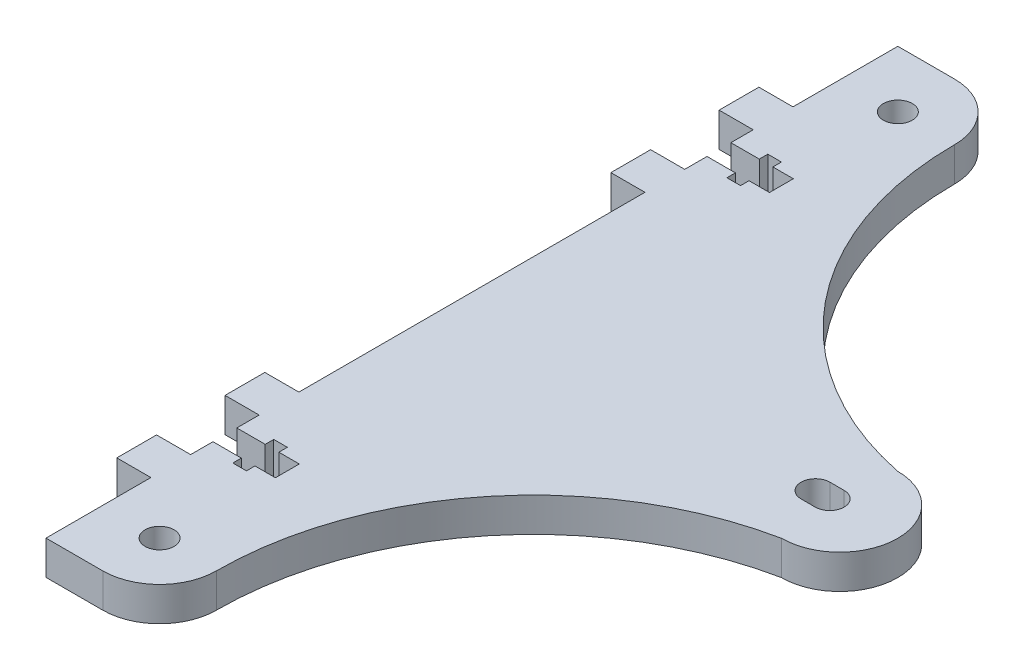
SolidWorks part; units mm, degrees
material "Клен"
ref_plane "Спереди" through (0, 0, 0) normal (0, 0, 1) x (1, 0, 0)
ref_plane "Сверху" through (0, 0, 0) normal (0, 1, 0) x (1, 0, 0)
ref_plane "Справа" through (0, 0, 0) normal (1, 0, 0) x (0, 0, -1)
sketch "Эскиз1" plane through (0, 0, 0) normal (0, 1, 0) x (1, 0, 0)
  line L0 (-41.181, -0.0464) -> (44.1026, -0.0464) construction
  line L9 (-35, -65) -> (-35, -75)
  line L11 (-35, -65) -> (-35, 65)
  line L12 (-35, -75) -> (-25, -75)
  line L14 (-35, 65) -> (-35, 75)
  line L15 (-35, 75) -> (-25, 75)
  arc A8 (-25, 75) -> (-15, 65) centre (-25, 65) cw
  arc A9 (-25, -75) -> (-15, -65) centre (-25, -65) ccw
  arc A10 (29.8091, 10.176) -> (29.8091, -10.2688) centre (29.8091, -0.0464) cw
  arc A13 (-15, -65) -> (29.8091, -10.2688) centre (40.8297, -65) cw
  arc A14 (-15, 65) -> (29.8091, 10.176) centre (40.9431, 65) ccw
  point P0 (0, 0)
extrude "Бобышка-Вытянуть1" add sketch "Эскиз1" along normal blind 6
sketch "Эскиз2" plane through (0, 0, 0) normal (0, -1, 0) x (1, 0, 0)
  line L4 (28, 0) -> (25.5, 0) construction
  line L5 (28, -2.55) -> (25.5, -2.55)
  line L6 (-46.1924, 0) -> (55.6646, 0) construction
  line L7 (28, 2.55) -> (25.5, 2.55)
  circle A0 centre (-25, -65) radius 2.55
  circle A5 centre (-25, 65) radius 2.55
  arc A6 (28, -2.55) -> (28, 2.55) centre (28, 0) ccw
  arc A7 (25.5, 2.55) -> (25.5, -2.55) centre (25.5, 0) ccw
  arc A8 (-25, -75) -> (-15, -65) centre (-25, -65) ccw construction
  point P13 (26.75, 0)
  dimension "D1" = 5.1
  dimension "D7" = 5.1
  dimension "D8" = 2.5
  dimension "D9" = 53
extrude "Вырез-Вытянуть1" cut sketch "Эскиз2" against normal through all
sketch "Эскиз21" plane through (15, 6, -43.5) normal (0, 1, 0) x (0, 0, -1)
  line L1 (-13.0318, 50) -> (-6.0318, 50)
  line L2 (-13.0318, 50) -> (-13.0318, 56)
  line L3 (-13.0318, 56) -> (-6.0318, 56)
  line L4 (-6.0318, 50) -> (-6.0318, 56)
  line L5 (13, 56) -> (-13, 56) construction
  line L6 (0, 53.4074) -> (0, -162.0434) construction
  line L7 (13.0318, 50) -> (6.0318, 50)
  line L8 (6.0318, 50) -> (6.0318, 56)
  line L9 (13.0318, 56) -> (6.0318, 56)
  line L10 (13.0318, 50) -> (13.0318, 56)
  dimension "D1" = 7
extrude "Бобышка-Вытянуть2" add sketch "Эскиз21" against normal blind 6
sketch "Эскиз31" plane through (15, 6, -43.5) normal (0, 1, 0) x (0, 0, -1)
  line L3 (-2.1, 45) -> (-3.6, 45)
  line L4 (-3.6, 45) -> (-3.6, 42.6)
  line L5 (-3.6, 42.6) -> (-2.1, 42.6)
  line L8 (0, 53.4074) -> (0, -162.0434) construction
  line L11 (3.6, 42.6) -> (2.1, 42.6)
  line L12 (3.6, 45) -> (3.6, 42.6)
  line L13 (2.1, 45) -> (3.6, 45)
  line L16 (-2.1, 45) -> (-2.1, 50)
  line L17 (-2.1, 50) -> (2.1, 50)
  line L18 (2.1, 50) -> (2.1, 45)
  line L19 (2.1, 42.6) -> (2.1, 39)
  line L20 (2.1, 39) -> (-2.1, 39)
  line L21 (-2.1, 39) -> (-2.1, 42.6)
  point P15 (0, 43.65)
  point P20 (0, 50)
  dimension "D2" = 7.2
  dimension "D3" = 2.4
  dimension "D4" = 4.2
extrude "Вырез-Вытянуть11" cut sketch "Эскиз31" against normal through all
other "Авто-элемент1<DIN967-4>"
sketch "Эскиз22" plane through (15, 0, -43.5) normal (0, -1, 0) x (0, 0, 1)
  line L1 (-13.0318, 50) -> (-6.0318, 50)
  line L2 (-13.0318, 50) -> (-13.0318, 56)
  line L3 (-13.0318, 56) -> (-6.0318, 56)
  line L4 (-6.0318, 50) -> (-6.0318, 56)
  line L5 (13, 56) -> (-13, 56) construction
  line L6 (0, 53.4074) -> (0, -162.0434) construction
  line L7 (13.0318, 50) -> (6.0318, 50)
  line L8 (6.0318, 50) -> (6.0318, 56)
  line L9 (13.0318, 56) -> (6.0318, 56)
  line L10 (13.0318, 50) -> (13.0318, 56)
  dimension "D1" = 7
extrude "Бобышка-Вытянуть21" add sketch "Эскиз22" against normal blind 6
other "Авто-элемент2<DIN967-5>"
sketch "Эскиз24" plane through (15, 0, 43.5) normal (0, -1, 0) x (0, 0, 1)
  line L1 (-13.0318, 50) -> (-6.0318, 50)
  line L2 (-13.0318, 50) -> (-13.0318, 56)
  line L3 (-13.0318, 56) -> (-6.0318, 56)
  line L4 (-6.0318, 50) -> (-6.0318, 56)
  line L5 (13, 56) -> (-13, 56) construction
  line L6 (0, 53.4074) -> (0, -162.0434) construction
  line L7 (13.0318, 50) -> (6.0318, 50)
  line L8 (6.0318, 50) -> (6.0318, 56)
  line L9 (13.0318, 56) -> (6.0318, 56)
  line L10 (13.0318, 50) -> (13.0318, 56)
  dimension "D1" = 7
extrude "Бобышка-Вытянуть23" add sketch "Эскиз24" against normal blind 6
sketch "Эскиз34" plane through (15, 0, 43.5) normal (0, -1, 0) x (0, 0, 1)
  line L3 (-2.1, 45) -> (-3.6, 45)
  line L4 (-3.6, 45) -> (-3.6, 42.6)
  line L5 (-3.6, 42.6) -> (-2.1, 42.6)
  line L8 (0, 53.4074) -> (0, -162.0434) construction
  line L11 (3.6, 42.6) -> (2.1, 42.6)
  line L12 (3.6, 45) -> (3.6, 42.6)
  line L13 (2.1, 45) -> (3.6, 45)
  line L16 (-2.1, 45) -> (-2.1, 50)
  line L17 (-2.1, 50) -> (2.1, 50)
  line L18 (2.1, 50) -> (2.1, 45)
  line L19 (2.1, 42.6) -> (2.1, 39)
  line L20 (2.1, 39) -> (-2.1, 39)
  line L21 (-2.1, 39) -> (-2.1, 42.6)
  point P15 (0, 43.65)
  point P20 (0, 50)
  dimension "D2" = 7.2
  dimension "D3" = 2.4
  dimension "D4" = 4.2
extrude "Вырез-Вытянуть14" cut sketch "Эскиз34" against normal through all
other "Авто-элемент4<DIN967-6>"
sketch "Эскиз25" plane through (15, 6, 43.5) normal (0, 1, 0) x (0, 0, -1)
  line L1 (-13.0318, 50) -> (-6.0318, 50)
  line L2 (-13.0318, 50) -> (-13.0318, 56)
  line L3 (-13.0318, 56) -> (-6.0318, 56)
  line L4 (-6.0318, 50) -> (-6.0318, 56)
  line L5 (13, 56) -> (-13, 56) construction
  line L6 (0, 53.4074) -> (0, -162.0434) construction
  line L7 (13.0318, 50) -> (6.0318, 50)
  line L8 (6.0318, 50) -> (6.0318, 56)
  line L9 (13.0318, 56) -> (6.0318, 56)
  line L10 (13.0318, 50) -> (13.0318, 56)
  dimension "D1" = 7
extrude "Бобышка-Вытянуть24" add sketch "Эскиз25" against normal blind 6
other "Авто-элемент5<DIN967-7>"
sketch "Эскиз26" plane through (15, 6, -43.5) normal (0, 1, 0) x (0, 0, -1)
  line L1 (-13.0318, 50) -> (-6.0318, 50)
  line L2 (-13.0318, 50) -> (-13.0318, 56)
  line L3 (-13.0318, 56) -> (-6.0318, 56)
  line L4 (-6.0318, 50) -> (-6.0318, 56)
  line L5 (13, 56) -> (-13, 56) construction
  line L6 (0, 53.4074) -> (0, -162.0434) construction
  line L7 (13.0318, 50) -> (6.0318, 50)
  line L8 (6.0318, 50) -> (6.0318, 56)
  line L9 (13.0318, 56) -> (6.0318, 56)
  line L10 (13.0318, 50) -> (13.0318, 56)
  dimension "D1" = 7
extrude "Бобышка-Вытянуть25" add sketch "Эскиз26" against normal blind 6
other "Авто-элемент6<DIN967-9>"
sketch "Эскиз27" plane through (15, 6, 43.5) normal (0, 1, 0) x (0, 0, -1)
  line L1 (-13.0318, 50) -> (-6.0318, 50)
  line L2 (-13.0318, 50) -> (-13.0318, 56)
  line L3 (-13.0318, 56) -> (-6.0318, 56)
  line L4 (-6.0318, 50) -> (-6.0318, 56)
  line L5 (13, 56) -> (-13, 56) construction
  line L6 (0, 53.4074) -> (0, -162.0434) construction
  line L7 (13.0318, 50) -> (6.0318, 50)
  line L8 (6.0318, 50) -> (6.0318, 56)
  line L9 (13.0318, 56) -> (6.0318, 56)
  line L10 (13.0318, 50) -> (13.0318, 56)
  dimension "D1" = 7
extrude "Бобышка-Вытянуть26" add sketch "Эскиз27" against normal blind 6
other "Авто-элемент7<DIN967-8>"
sketch "Эскиз28" plane through (15, 0, -43.5) normal (0, -1, 0) x (0, 0, 1)
  line L1 (-13.0318, 50) -> (-6.0318, 50)
  line L2 (-13.0318, 50) -> (-13.0318, 56)
  line L3 (-13.0318, 56) -> (-6.0318, 56)
  line L4 (-6.0318, 50) -> (-6.0318, 56)
  line L5 (13, 56) -> (-13, 56) construction
  line L6 (0, 53.4074) -> (0, -162.0434) construction
  line L7 (13.0318, 50) -> (6.0318, 50)
  line L8 (6.0318, 50) -> (6.0318, 56)
  line L9 (13.0318, 56) -> (6.0318, 56)
  line L10 (13.0318, 50) -> (13.0318, 56)
  dimension "D1" = 7
extrude "Бобышка-Вытянуть27" add sketch "Эскиз28" against normal blind 6
other "Авто-элемент8<DIN967-11>"
sketch "Эскиз29" plane through (15, 0, 43.5) normal (0, -1, 0) x (0, 0, 1)
  line L1 (-13.0318, 50) -> (-6.0318, 50)
  line L2 (-13.0318, 50) -> (-13.0318, 56)
  line L3 (-13.0318, 56) -> (-6.0318, 56)
  line L4 (-6.0318, 50) -> (-6.0318, 56)
  line L5 (13, 56) -> (-13, 56) construction
  line L6 (0, 53.4074) -> (0, -162.0434) construction
  line L7 (13.0318, 50) -> (6.0318, 50)
  line L8 (6.0318, 50) -> (6.0318, 56)
  line L9 (13.0318, 56) -> (6.0318, 56)
  line L10 (13.0318, 50) -> (13.0318, 56)
  dimension "D1" = 7
extrude "Бобышка-Вытянуть28" add sketch "Эскиз29" against normal blind 6
other "Авто-элемент9<DIN967-10>"
